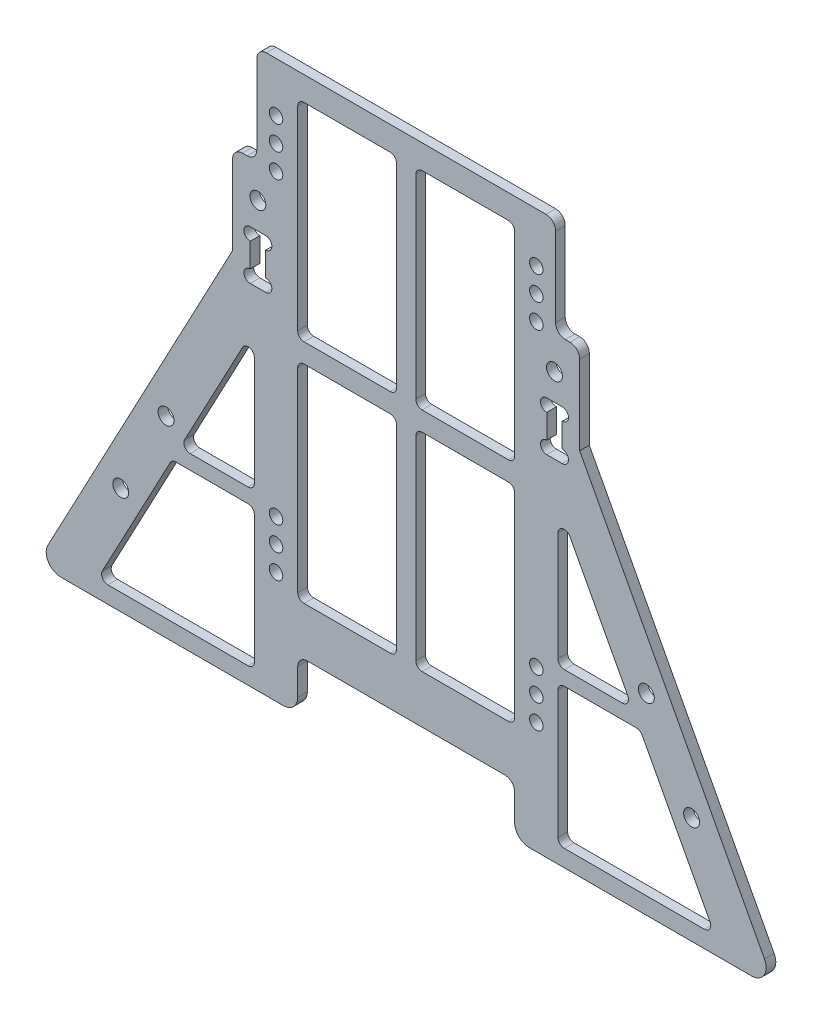
SolidWorks part; units mm, degrees
material "Thornel Mat VMA"
ref_plane "前视基准面" through (0, 0, 0) normal (0, 0, 1) x (1, 0, 0)
ref_plane "上视基准面" through (0, 0, 0) normal (0, 1, 0) x (1, 0, 0)
ref_plane "右视基准面" through (0, 0, 0) normal (1, 0, 0) x (0, 0, -1)
sketch "草图1" plane through (0, 0, 0) normal (0, 0, 1) x (1, 0, 0)
  line L1 (-36, -75) -> (36, -75)
  line L2 (-36, -75) -> (-36, 75)
  line L3 (-36, 75) -> (36, 75)
  line L4 (36, -75) -> (36, 75)
  line L5 (-36, -75) -> (36, 75) construction
  line L6 (-36, 75) -> (36, -75) construction
  point P0 (0, 0)
  dimension "D1" = 72
  dimension "D2" = 150
extrude "凸台-拉伸1" add sketch "草图1" along normal mid plane 2
sketch "草图2" plane through (0, 0, -1) normal (0, 0, -1) x (-1, 0, 0)
  line L2 (0, 0) -> (0, 94.0578) construction
  circle A4 centre (-27, -12.3) radius 1.4
  circle A5 centre (27, -12.3) radius 1.4
  circle A6 centre (27, 59.7) radius 1.4
  circle A7 centre (-27, 59.7) radius 1.4
  dimension "D1" = 2.8
  dimension "D2" = 54
  dimension "D3" = 72
  dimension "D4" = 54
  dimension "D5" = 59.7
extrude "切除-拉伸1" cut sketch "草图2" against normal blind 2
pattern_linear "阵列(线性)1" count 2 spacing 5 along (0, -1, 0) of "切除-拉伸1"
pattern_linear "阵列(线性)2" count 2 spacing 5 along (0, 1, 0) of "切除-拉伸1"
sketch "草图3" plane through (0, 0, -1) normal (0, 0, -1) x (-1, 0, 0)
  line L1 (-29.25, 24) -> (33, 24) construction
  line L2 (-36, -75) -> (-36, 75) construction
  line L3 (-39, 24) -> (-33, 24)
  line L4 (-39, 24) -> (-39, 42)
  line L5 (-39, 42) -> (-33, 42)
  line L6 (-33, 24) -> (-33, 42)
  line L7 (-39, 24) -> (-33, 42) construction
  line L8 (-39, 42) -> (-33, 24) construction
  line L9 (0, 0) -> (0, 59.9175) construction
  line L10 (39, 42) -> (33, 42)
  line L11 (33, 24) -> (33, 42)
  line L12 (39, 24) -> (33, 24)
  line L13 (39, 24) -> (39, 42)
  line L14 (39, -26) -> (33, -44) construction
  line L15 (-39, -44) -> (-33, -44)
  line L16 (-39, -44) -> (-39, -26)
  line L17 (-39, -26) -> (-33, -26)
  line L18 (-33, -44) -> (-33, -26)
  line L19 (-39, -44) -> (-33, -26) construction
  line L20 (-39, -26) -> (-33, -44) construction
  line L21 (39, -44) -> (33, -26) construction
  line L22 (33, -44) -> (33, -26)
  line L23 (39, -26) -> (33, -26)
  line L24 (39, -44) -> (39, -26)
  line L25 (39, -44) -> (33, -44)
  point P2 (-36, 33)
  point P15 (-36, -35)
  point P24 (36, -35)
  dimension "D1" = 18
  dimension "D2" = 3
  dimension "D3" = 3
  dimension "D4" = 18
  dimension "D5" = 35
extrude "凸台-拉伸2" [suppressed] add sketch "草图3" against normal up to surface (2 mm away)
sketch "草图5" plane through (0, 0, -1) normal (0, 0, -1) x (-1, 0, 0)
  line L0 (26.25, -52.5) -> (-26.25, -52.5) construction
  line L1 (-26.25, -52.5) -> (-26.25, -32.5) construction
  line L2 (-26.25, -32.5) -> (26.25, -32.5) construction
  line L3 (26.25, -32.5) -> (26.25, -52.5) construction
  line L4 (0, -32.5) -> (0, 0) construction
  circle A4 centre (-26.25, -32.5) radius 1.65
  circle A5 centre (-26.25, -52.5) radius 1.65
  circle A6 centre (26.25, -32.5) radius 1.65
  circle A7 centre (26.25, -52.5) radius 1.65
  dimension "D1" = 3.3
  dimension "D2" = 20
  dimension "D3" = 32.5
  dimension "D4" = 52.5
extrude "切除-拉伸2" [suppressed] cut sketch "草图5" against normal blind 10
sketch "草图6" [suppressed] plane through (0, 0, -1) normal (0, 0, -1) x (-1, 0, 0)
  line L1 (35.25, -26) -> (32.25, -26)
  line L2 (35.25, -26) -> (35.25, -44)
  line L3 (35.25, -44) -> (32.25, -44)
  line L4 (32.25, -26) -> (32.25, -44)
  line L5 (-35.25, -26) -> (-32.25, -26)
  line L6 (-35.25, -26) -> (-35.25, -44)
  line L7 (-35.25, -44) -> (-32.25, -44)
  line L8 (-32.25, -26) -> (-32.25, -44)
extrude "切除-拉伸3" [suppressed] cut sketch "草图6" against normal blind 10
sketch "草图7" plane through (0, 0, -1) normal (0, 0, -1) x (-1, 0, 0)
  line L1 (36, -75) -> (-74, -75)
  line L2 (36, -75) -> (36, -172.0167)
  line L3 (36, -172.0167) -> (-74, -172.0167)
  line L4 (-74, -75) -> (-74, -172.0167)
  line L5 (-36, -75) -> (-36, 75) construction
  line L6 (-74, -75) -> (-36, -75)
  line L7 (-74, -75) -> (-74, -45)
  line L8 (-74, -45) -> (-36, -45)
  line L9 (-36, -75) -> (-36, -45)
  dimension "D1" = 97.0167
  dimension "D2" = 30
  dimension "D3" = 110
extrude "凸台-拉伸3" [suppressed] add sketch "草图7" against normal up to surface (2 mm away)
sketch "草图8" plane through (0, 0, -1) normal (0, 0, -1) x (-1, 0, 0)
  line L0 (36, 75) -> (36, -75) construction
  line L1 (-36, -75) -> (36, -75)
  line L2 (-36, -75) -> (-36, -79.8)
  line L3 (-36, -79.8) -> (36, -79.8)
  line L4 (36, -75) -> (36, -79.8)
  dimension "D1" = 4.8
extrude "凸台-拉伸4" [suppressed] add sketch "草图8" against normal up to surface (2 mm away)
sketch "草图9" plane through (0, 0, 1) normal (0, 0, 1) x (1, 0, 0)
  line L0 (36, -75) -> (36, 75) construction
  line L1 (-36, -75) -> (36, -75)
  line L2 (-36, -75) -> (-36, -67.5)
  line L3 (-36, -67.5) -> (36, -67.5)
  line L4 (36, -75) -> (36, -67.5)
  dimension "D1" = 7.5
extrude "切除-拉伸4" cut sketch "草图9" against normal blind 5.5
sketch "草图11" plane through (0, 0, -1) normal (0, 0, -1) x (-1, 0, 0)
  line L1 (-36, 36) -> (-78, -43.0167)
  line L3 (-78, -43.0167) -> (-36, -43.0167)
  line L4 (-36, -43.0167) -> (-36, 36)
  line L5 (-36, -67.5) -> (-36, 75) construction
  line L6 (0, 0) -> (0, -53.8251) construction
  line L7 (36, -43.0167) -> (36, 36)
  line L8 (78, -43.0167) -> (36, -43.0167)
  line L9 (36, 36) -> (78, -43.0167)
extrude "凸台-拉伸5" add sketch "草图11" against normal up to surface (2 mm away) up to face at (25.6, 64.7, 1)
sketch "草图12" plane through (0, 0, 1) normal (0, 0, 1) x (1, 0, 0)
  line L0 (36, -67.5) -> (-36, -67.5) construction
  line L1 (-36, -91.9833) -> (36, -91.9833)
  line L2 (-36, -91.9833) -> (-36, -43.0167)
  line L3 (-36, -43.0167) -> (36, -43.0167)
  line L4 (36, -91.9833) -> (36, -43.0167)
  line L5 (-36, -91.9833) -> (36, -43.0167) construction
  line L6 (-36, -43.0167) -> (36, -91.9833) construction
  point P0 (0, -67.5)
extrude "切除-拉伸5" cut sketch "草图12" against normal blind 10
sketch "草图14" plane through (0, 0, -1) normal (0, 0, -1) x (-1, 0, 0)
  line L0 (0, 0) -> (-49.823, -0.6588) construction
  line L1 (0, 0) -> (0, -18.3191) construction
  line L2 (0, -18.3191) -> (-59.21, -18.3191) construction
  circle A2 centre (-49.823, -0.6588) radius 1.65
  circle A3 centre (-59.21, -18.3191) radius 1.65
  circle A4 centre (49.823, -0.6588) radius 1.65
  circle A5 centre (59.21, -18.3191) radius 1.65
  dimension "D4" = 3.3
  dimension "D1" = 49.823
  dimension "D2" = 18.3191
  dimension "D3" = 0.6588
  dimension "D5" = 59.21
extrude "切除-拉伸6" cut sketch "草图14" against normal blind 10
sketch "草图15" plane through (0, 0, -1) normal (0, 0, -1) x (-1, 0, 0)
  line L8 (29.25, 32) -> (32.25, 32) construction
  line L9 (32.25, 32) -> (32.25, 42) construction
  line L10 (32.25, 42) -> (29.25, 42) construction
  line L11 (29.25, 42) -> (29.25, 32) construction
  line L12 (-32.2673, 32) -> (-29.2673, 32) construction
  line L13 (-29.2673, 32) -> (-29.2673, 42) construction
  line L14 (-29.2673, 42) -> (-32.2673, 42) construction
  line L15 (-32.2673, 42) -> (-32.2673, 32) construction
  line L16 (29.15, 31.9) -> (32.35, 31.9)
  line L17 (32.35, 31.9) -> (32.35, 42.1)
  line L18 (32.35, 42.1) -> (29.15, 42.1)
  line L19 (29.15, 42.1) -> (29.15, 31.9)
  line L20 (-32.3673, 31.9) -> (-29.1673, 31.9)
  line L21 (-29.1673, 31.9) -> (-29.1673, 42.1)
  line L22 (-29.1673, 42.1) -> (-32.3673, 42.1)
  line L23 (-32.3673, 42.1) -> (-32.3673, 31.9)
  dimension "D1" = 0.1
  dimension "D2" = 0.1
extrude "切除-拉伸7" cut sketch "草图15" against normal blind 10
sketch "草图16" plane through (0, 0, -1) normal (0, 0, -1) x (-1, 0, 0)
  line L0 (-29.1673, 31.9) -> (-29.1673, 42.1) construction
  line L2 (-32.3673, 42.1) -> (-32.3673, 31.9) construction
  line L3 (0, 0) -> (0, 57.812) construction
  circle A0 centre (-29.1673, 40.8) radius 1.3
  circle A2 centre (-32.3673, 40.8) radius 1.3
  circle A3 centre (-32.3673, 33.2) radius 1.3
  circle A4 centre (-29.1673, 33.2) radius 1.3
  circle A5 centre (29.1673, 33.2) radius 1.3
  circle A6 centre (32.3673, 33.2) radius 1.3
  circle A7 centre (32.3673, 40.8) radius 1.3
  circle A8 centre (29.1673, 40.8) radius 1.3
  dimension "D1" = 2.6
extrude "切除-拉伸8" cut sketch "草图16" against normal blind 10
sketch "草图17" plane through (0, 0, -1) normal (0, 0, -1) x (-1, 0, 0)
  line L0 (-30.7673, 42.1) -> (-30.7673, 47.6) construction
  line L1 (-29.1673, 42.1) -> (-32.3673, 42.1) construction
  line L2 (0, 0) -> (0, 97.2929) construction
  line L3 (30.7673, 42.1) -> (30.7673, 47.6) construction
  circle A0 centre (-30.7673, 47.6) radius 1.65
  circle A1 centre (30.7673, 47.6) radius 1.65
  dimension "D1" = 3.3
  dimension "D2" = 5.5
extrude "切除-拉伸9" cut sketch "草图17" against normal blind 10
fillet "圆角1" radius 2 2 edges at (-36, 75, 0) (36, 75, 0)
sketch "草图18" plane through (0, 0, -1) normal (0, 0, -1) x (-1, 0, 0)
  line L0 (-22.5, 70) -> (-22.5, -20)
  line L1 (-22.5, -20) -> (22.5, -20)
  line L2 (22.5, -20) -> (22.5, 70)
  line L3 (22.5, 70) -> (-22.5, 70)
  line L4 (-34, 75) -> (34, 75) construction
  line L5 (0, 70) -> (0, -20) construction
  line L6 (-22.5, 25) -> (22.5, 25) construction
  line L7 (-22.5, 23) -> (22.5, 23)
  line L8 (-22.5, 27) -> (22.5, 27)
  line L9 (-2, 70) -> (-2, -20)
  line L10 (2, 70) -> (2, -20)
  circle A0 centre (-27, 64.7) radius 1.4 construction
  circle A1 centre (27, 64.7) radius 1.4 construction
  dimension "D3" = 4.5
  dimension "D1" = 5
  dimension "D2" = 90
  dimension "D4" = 4.5
  dimension "D5" = 2
  dimension "D6" = 2
  dimension "D7" = 2
  dimension "D8" = 2
extrude "切除-拉伸10" cut sketch "草图18" against normal blind 10 contours L3 L10 L8 L2 | L9 L3 L0 L8 | L9 L7 L0 L1 | L7 L10 L1 L2
sketch "草图19" plane through (0, 0, -1) normal (0, 0, -1) x (-1, 0, 0)
  line L0 (-31.5, 24.2253) -> (-64.0522, -37.0167)
  line L1 (-64.0522, -37.0167) -> (-31.5, -37.0167)
  line L2 (-31.5, -37.0167) -> (-31.5, 24.2253)
  line L3 (-36, 36) -> (-78, -43.0167) construction
  line L4 (-78, -43.0167) -> (78, -43.0167) construction
  line L5 (-31.5, -6.3957) -> (-47.7761, -6.3957) construction
  line L6 (-31.5, -4.8957) -> (-47.7761, -4.8957)
  line L7 (-31.5, -7.8957) -> (-48.5734, -7.8957)
  line L8 (0, 0) -> (0, -62.4691) construction
  line L9 (31.5, -6.3957) -> (47.7761, -6.3957) construction
  line L10 (31.5, -7.8957) -> (48.5734, -7.8957)
  line L11 (31.5, -4.8957) -> (47.7761, -4.8957)
  line L12 (31.5, -37.0167) -> (31.5, 24.2253)
  line L13 (64.0522, -37.0167) -> (31.5, -37.0167)
  line L14 (31.5, 24.2253) -> (64.0522, -37.0167)
  line L15 (-31.5, -7.8957) -> (-47.7761, -7.8957) construction
  circle A0 centre (-27, -12.3) radius 1.4 construction
  circle A1 centre (-49.823, -0.6588) radius 1.65 construction
  dimension "D1" = 4.5
  dimension "D2" = 4.5
  dimension "D3" = 6
  dimension "D4" = 1.5
  dimension "D5" = 1.5
extrude "切除-拉伸11" cut sketch "草图19" against normal blind 10 contours L2 L7 L0 L1 | L6 L2 L0 | L14 L12 L11 | L14 L10 L12 L13
fillet "圆角2" radius 1.3 30 edges at (-64.0522, -37.0167, 0) (-31.5, -37.0167, 0) (-31.5, -7.8957, 0) (-48.5734, -7.8957, 0) (46.9788, -4.8957, 0) (31.5, 24.2253, 0) (31.5, -4.8957, 0) (48.5734, -7.8957, 0) (31.5, -7.8957, 0) (2, -20, 0) (22.5, -20, 0) (22.5, 23, 0) (2, 23, 0) (-22.5, 27, 0) (-2, 27, 0) (-2, 70, 0) (-22.5, 70, 0) (2, 27, 0) (22.5, 27, 0) (22.5, 70, 0) (2, 70, 0) (-22.5, 23, 0) (-22.5, -20, 0) (-2, -20, 0) (-2, 23, 0) (-46.9788, -4.8957, 0) (-31.5, -4.8957, 0) (-31.5, 24.2253, 0) (64.0522, -37.0167, 0) (31.5, -37.0167, 0)
sketch "草图20" plane through (0, 0, -1) normal (0, 0, -1) x (-1, 0, 0)
  line L0 (-78, -43.0167) -> (78, -43.0167) construction
  line L1 (-22.5, -56.0333) -> (22.5, -56.0333)
  line L2 (-22.5, -56.0333) -> (-22.5, -30)
  line L3 (-22.5, -30) -> (22.5, -30)
  line L4 (22.5, -56.0333) -> (22.5, -30)
  line L5 (-22.5, -56.0333) -> (22.5, -30) construction
  line L6 (-22.5, -30) -> (22.5, -56.0333) construction
  line L7 (3.3, -20) -> (21.2, -20) construction
  line L8 (-22.5, 21.7) -> (-22.5, -18.7) construction
  point P0 (0, -43.0167)
  dimension "D1" = 10
extrude "切除-拉伸12" cut sketch "草图20" against normal blind 10
fillet "圆角3" radius 2 2 edges at (-22.5, -30, 0) (22.5, -30, 0)
sketch "草图21" plane through (0, 0, -1) normal (0, 0, -1) x (-1, 0, 0)
  line L0 (-36, 54.5) -> (-31, 54.5)
  line L1 (-36, 36) -> (-36, 73) construction
  line L2 (-31, 54.5) -> (-31, 75)
  line L3 (-34, 75) -> (34, 75) construction
  line L4 (31, 75) -> (36, 75)
  line L5 (31, 75) -> (31, 54.5)
  line L6 (31, 54.5) -> (36, 54.5)
  line L7 (36, 73) -> (36, 36) construction
  line L8 (-31, 75) -> (-36, 75)
  line L9 (-36, 75) -> (-36, 54.5)
  line L10 (36, 75) -> (36, 54.5)
  circle A0 centre (27, 64.7) radius 1.4 construction
  circle A1 centre (-27, 64.7) radius 1.4 construction
  dimension "D1" = 4
  dimension "D2" = 4
extrude "切除-拉伸13" cut sketch "草图21" against normal blind 10
fillet "圆角4" radius 2 6 edges at (36, 54.5, 0) (-31, 75, 0) (31, 75, 0) (31, 54.5, 0) (-31, 54.5, 0) (-36, 54.5, 0)
sketch "草图22" plane through (0, 0, -1) normal (0, 0, -1) x (-1, 0, 0)
  line L1 (78, -43.0167) -> (-78, -43.0167)
  line L2 (78, -43.0167) -> (78, -40.5167)
  line L3 (78, -40.5167) -> (-78, -40.5167)
  line L4 (-78, -43.0167) -> (-78, -40.5167)
  dimension "D1" = 2.5
extrude "切除-拉伸14" cut sketch "草图22" against normal through all
fillet "圆角5" radius 3 4 edges at (76.6712, -40.5167, 0) (22.5, -40.5167, 0) (-22.5, -40.5167, 0) (-76.6712, -40.5167, 0)
